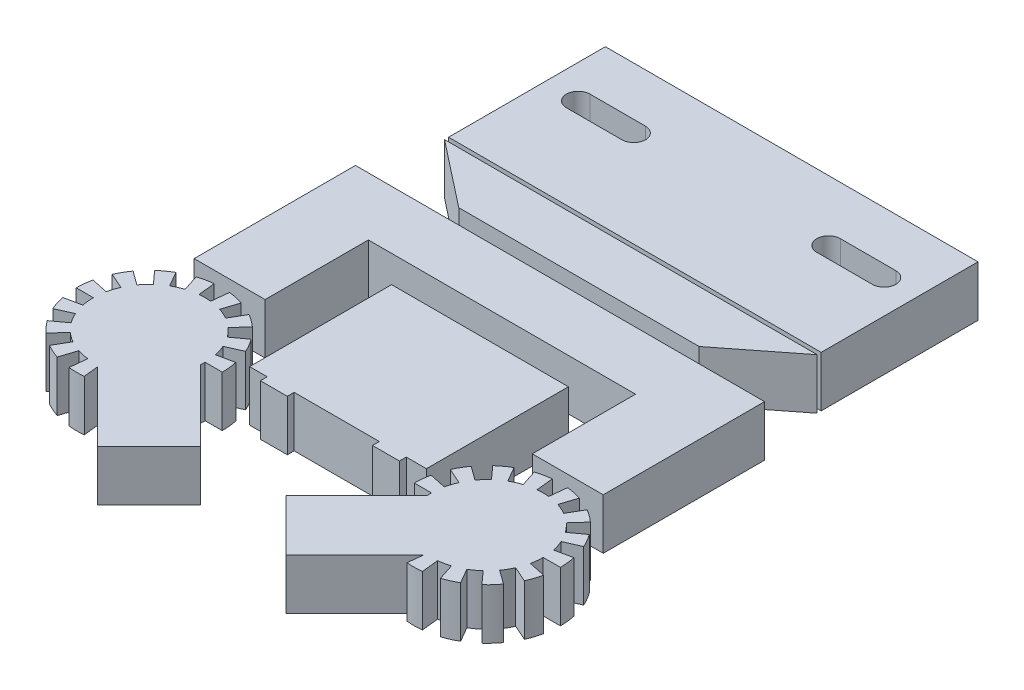
SolidWorks part; units mm, degrees
ref_plane "Front Plane" through (0, 0, 0) normal (0, 0, 1) x (1, 0, 0)
ref_plane "Top Plane" through (0, 0, 0) normal (0, 1, 0) x (1, 0, 0)
ref_plane "Right Plane" through (0, 0, 0) normal (1, 0, 0) x (0, 0, -1)
sketch "Sketch1" plane through (0, 0, 0) normal (0, 1, 0) x (1, 0, 0)
  line L0 (-41.1091, 4.4545) -> (-41.1091, 36.2727)
  line L1 (-41.1091, 36.2727) -> (39.5818, 36.2727)
  line L2 (39.5818, 36.2727) -> (39.5818, 4.4545)
  line L3 (39.5818, 4.4545) -> (25.5818, 4.4545)
  line L4 (25.5818, 4.4545) -> (25.5818, 24.8182)
  line L5 (25.5818, 24.8182) -> (-27.1091, 24.8182)
  line L6 (-27.1091, 24.8182) -> (-27.1091, 4.4545)
  line L7 (-27.1091, 4.4545) -> (-41.1091, 4.4545)
  line L8 (-32.1391, -23.6063) -> (-18.5818, -37.1636)
  line L9 (-17.1818, 19.4727) -> (17.6909, 19.4727)
  line L10 (-17.1818, 19.4727) -> (-17.1818, -8.5273)
  line L11 (-17.1818, -8.5273) -> (17.6909, -8.5273)
  line L12 (17.6909, 19.4727) -> (17.6909, -8.5273)
  line L13 (-18.5818, -37.1636) -> (-8.4, -26.9818)
  line L14 (-8.4, -26.9818) -> (-22.3545, -13.0274)
  line L15 (0, 0) -> (0, 56.6534) construction
  line L16 (23.2736, -7.685) -> (20.1863, -6.3104)
  line L17 (24.4256, -5.6897) -> (21.6916, -3.7033)
  line L18 (25.9672, -3.9776) -> (23.7059, -1.4662)
  line L55 (27.8311, -2.6234) -> (26.1414, 0.3033)
  line L56 (29.9359, -1.6863) -> (28.8916, 1.5278)
  line L57 (-22.3209, -12.1674) -> (-18.9414, -12.1674) construction
  line L58 (-22.5617, -9.8761) -> (-19.2561, -9.1735) construction
  line L60 (-22.5617, -9.8761) -> (-19.2561, -9.1735)
  line L61 (-22.3209, -12.1674) -> (-18.9414, -12.1674)
  line L67 (-32.1391, -23.6063) -> (-31.8362, -26.4886)
  line L68 (-34.4934, -23.1276) -> (-34.8466, -26.4886)
  line L69 (-36.7469, -22.6486) -> (-37.7912, -25.8627)
  line L70 (-38.8517, -21.7115) -> (-40.5414, -24.6382)
  line L71 (-40.7156, -20.3573) -> (-42.9769, -22.8687)
  line L72 (-42.2572, -18.6452) -> (-44.9912, -20.6315)
  line L73 (-43.4092, -16.6499) -> (-46.4965, -18.0244)
  line L74 (-44.1211, -14.4587) -> (-47.4267, -15.1614)
  line L75 (-44.3619, -12.1674) -> (-47.7414, -12.1674)
  line L76 (-44.1211, -9.8761) -> (-47.4267, -9.1735)
  line L77 (-43.4092, -7.685) -> (-46.4965, -6.3104)
  line L78 (-42.2572, -5.6897) -> (-44.9912, -3.7033)
  line L79 (-40.7156, -3.9776) -> (-42.9769, -1.4662)
  line L80 (-38.8517, -2.6234) -> (-40.5414, 0.3033)
  line L81 (-36.7469, -1.6863) -> (-37.7912, 1.5278)
  line L82 (-34.4934, -1.2073) -> (-34.8466, 2.1537)
  line L83 (-32.1894, -1.2073) -> (-31.8362, 2.1537)
  line L84 (-29.9359, -1.6863) -> (-28.8916, 1.5278)
  line L85 (-27.8311, -2.6234) -> (-26.1414, 0.3033)
  line L86 (-25.9672, -3.9776) -> (-23.7059, -1.4662)
  line L87 (-24.4256, -5.6897) -> (-21.6916, -3.7033)
  line L88 (-23.2736, -7.685) -> (-20.1863, -6.3104)
  line L89 (32.1894, -1.2073) -> (31.8362, 2.1537)
  line L90 (34.4934, -1.2073) -> (34.8466, 2.1537)
  line L91 (36.7469, -1.6863) -> (37.7912, 1.5278)
  line L92 (38.8517, -2.6234) -> (40.5414, 0.3033)
  line L93 (40.7156, -3.9776) -> (42.9769, -1.4662)
  line L94 (42.2572, -5.6897) -> (44.9912, -3.7033)
  line L95 (43.4092, -7.685) -> (46.4965, -6.3104)
  line L96 (22.5617, -9.8761) -> (19.2561, -9.1735) construction
  line L97 (22.3209, -12.1674) -> (18.9414, -12.1674) construction
  line L98 (44.1211, -9.8761) -> (47.4267, -9.1735)
  line L99 (44.3619, -12.1674) -> (47.7414, -12.1674)
  line L100 (44.1211, -14.4587) -> (47.4267, -15.1614)
  line L101 (43.4092, -16.6499) -> (46.4965, -18.0244)
  line L102 (42.2572, -18.6452) -> (44.9912, -20.6315)
  line L103 (40.7156, -20.3573) -> (42.9769, -22.8687)
  line L104 (38.8517, -21.7115) -> (40.5414, -24.6382)
  line L105 (36.7469, -22.6486) -> (37.7912, -25.8627)
  line L106 (34.4934, -23.1276) -> (34.8466, -26.4886)
  line L107 (32.1391, -23.6063) -> (31.8362, -26.4886)
  line L108 (22.3209, -12.1674) -> (18.9414, -12.1674)
  line L109 (22.5617, -9.8761) -> (19.2561, -9.1735)
  line L110 (8.4, -26.9818) -> (22.3545, -13.0274)
  line L111 (18.5818, -37.1636) -> (8.4, -26.9818)
  line L112 (32.1391, -23.6063) -> (18.5818, -37.1636)
  line L113 (23.7059, 39.2427) -> (-23.7059, 39.2427)
  line L114 (-23.7059, 39.2427) -> (-36.7469, 49.4769)
  line L115 (-36.7469, 49.4769) -> (36.7469, 49.4769)
  line L116 (36.7469, 50.2767) -> (-36.7469, 50.2767)
  line L117 (-36.7469, 50.2767) -> (-36.7469, 81.202)
  line L118 (-36.7469, 81.202) -> (36.7469, 81.202)
  line L119 (-30.1628, 69.2589) -> (-19.2166, 69.2589) construction
  line L122 (-30.1628, 71.5881) -> (-19.2166, 71.5881)
  line L123 (-30.1628, 66.9297) -> (-19.2166, 66.9297)
  line L124 (36.7469, 50.2767) -> (36.7469, 81.202)
  line L125 (23.7059, 39.2427) -> (36.7469, 49.4769)
  line L126 (30.1628, 69.2589) -> (19.2166, 69.2589) construction
  line L127 (30.1628, 71.5881) -> (19.2166, 71.5881)
  line L128 (30.1628, 66.9297) -> (19.2166, 66.9297)
  line L129 (13.7109, -9.8761) -> (8.4, -9.8761)
  line L130 (-13.7109, -8.5273) -> (-8.4, -8.5273)
  line L131 (-13.7109, -8.5273) -> (-13.7109, -9.8761)
  line L132 (-13.7109, -9.8761) -> (-8.4, -9.8761)
  line L133 (-8.4, -8.5273) -> (-8.4, -9.8761)
  line L134 (8.4, -8.5273) -> (8.4, -9.8761)
  line L135 (13.7109, -8.5273) -> (8.4, -8.5273)
  line L136 (13.7109, -8.5273) -> (13.7109, -9.8761)
  arc A32 (-18.9414, -12.1674) -> (-19.2561, -9.1735) centre (-33.3414, -12.1674) ccw
  arc A33 (-22.5617, -9.8761) -> (-23.2736, -7.685) centre (-33.3414, -12.1674) ccw
  arc A34 (-22.3545, -13.0274) -> (-22.3209, -12.1674) centre (-33.3414, -12.1674) ccw
  arc A41 (-34.8466, -26.4886) -> (-31.8362, -26.4886) centre (-33.3414, -12.1674) ccw
  arc A42 (-36.7469, -22.6486) -> (-34.4934, -23.1276) centre (-33.3414, -12.1674) ccw
  arc A43 (-40.5414, -24.6382) -> (-37.7912, -25.8627) centre (-33.3414, -12.1674) ccw
  arc A44 (-40.7156, -20.3573) -> (-38.8517, -21.7115) centre (-33.3414, -12.1674) ccw
  arc A45 (-44.9912, -20.6315) -> (-42.9769, -22.8687) centre (-33.3414, -12.1674) ccw
  arc A46 (-43.4092, -16.6499) -> (-42.2572, -18.6452) centre (-33.3414, -12.1674) ccw
  arc A47 (-47.4267, -15.1614) -> (-46.4965, -18.0244) centre (-33.3414, -12.1674) ccw
  arc A48 (-44.3619, -12.1674) -> (-44.1211, -14.4587) centre (-33.3414, -12.1674) ccw
  arc A49 (-47.4267, -9.1735) -> (-47.7414, -12.1674) centre (-33.3414, -12.1674) ccw
  arc A50 (-43.4092, -7.685) -> (-44.1211, -9.8761) centre (-33.3414, -12.1674) ccw
  arc A51 (-44.9912, -3.7033) -> (-46.4965, -6.3104) centre (-33.3414, -12.1674) ccw
  arc A52 (-40.7156, -3.9776) -> (-42.2572, -5.6897) centre (-33.3414, -12.1674) ccw
  arc A53 (-40.5414, 0.3033) -> (-42.9769, -1.4662) centre (-33.3414, -12.1674) ccw
  arc A54 (-36.7469, -1.6863) -> (-38.8517, -2.6234) centre (-33.3414, -12.1674) ccw
  arc A55 (-34.8466, 2.1537) -> (-37.7912, 1.5278) centre (-33.3414, -12.1674) ccw
  arc A56 (-32.1894, -1.2073) -> (-34.4934, -1.2073) centre (-33.3414, -12.1674) ccw
  arc A57 (-28.8916, 1.5278) -> (-31.8362, 2.1537) centre (-33.3414, -12.1674) ccw
  arc A58 (-27.8311, -2.6234) -> (-29.9359, -1.6863) centre (-33.3414, -12.1674) ccw
  arc A59 (-23.7059, -1.4662) -> (-26.1414, 0.3033) centre (-33.3414, -12.1674) ccw
  arc A60 (-24.4256, -5.6897) -> (-25.9672, -3.9776) centre (-33.3414, -12.1674) ccw
  arc A61 (-20.1863, -6.3104) -> (-21.6916, -3.7033) centre (-33.3414, -12.1674) ccw
  arc A62 (20.1863, -6.3104) -> (21.6916, -3.7033) centre (33.3414, -12.1674) cw
  arc A63 (24.4256, -5.6897) -> (25.9672, -3.9776) centre (33.3414, -12.1674) cw
  arc A64 (23.7059, -1.4662) -> (26.1414, 0.3033) centre (33.3414, -12.1674) cw
  arc A65 (27.8311, -2.6234) -> (29.9359, -1.6863) centre (33.3414, -12.1674) cw
  arc A66 (28.8916, 1.5278) -> (31.8362, 2.1537) centre (33.3414, -12.1674) cw
  arc A67 (32.1894, -1.2073) -> (34.4934, -1.2073) centre (33.3414, -12.1674) cw
  arc A68 (34.8466, 2.1537) -> (37.7912, 1.5278) centre (33.3414, -12.1674) cw
  arc A69 (36.7469, -1.6863) -> (38.8517, -2.6234) centre (33.3414, -12.1674) cw
  arc A70 (40.5414, 0.3033) -> (42.9769, -1.4662) centre (33.3414, -12.1674) cw
  arc A71 (40.7156, -3.9776) -> (42.2572, -5.6897) centre (33.3414, -12.1674) cw
  arc A72 (44.9912, -3.7033) -> (46.4965, -6.3104) centre (33.3414, -12.1674) cw
  arc A73 (47.4267, -9.1735) -> (47.7414, -12.1674) centre (33.3414, -12.1674) cw
  arc A74 (47.4267, -15.1614) -> (46.4965, -18.0244) centre (33.3414, -12.1674) cw
  arc A75 (43.4092, -7.685) -> (44.1211, -9.8761) centre (33.3414, -12.1674) cw
  arc A76 (44.3619, -12.1674) -> (44.1211, -14.4587) centre (33.3414, -12.1674) cw
  arc A77 (43.4092, -16.6499) -> (42.2572, -18.6452) centre (33.3414, -12.1674) cw
  arc A78 (44.9912, -20.6315) -> (42.9769, -22.8687) centre (33.3414, -12.1674) cw
  arc A79 (40.7156, -20.3573) -> (38.8517, -21.7115) centre (33.3414, -12.1674) cw
  arc A80 (40.5414, -24.6382) -> (37.7912, -25.8627) centre (33.3414, -12.1674) cw
  arc A81 (36.7469, -22.6486) -> (34.4934, -23.1276) centre (33.3414, -12.1674) cw
  arc A82 (34.8466, -26.4886) -> (31.8362, -26.4886) centre (33.3414, -12.1674) cw
  arc A83 (22.3545, -13.0274) -> (22.3209, -12.1674) centre (33.3414, -12.1674) cw
  arc A84 (22.5617, -9.8761) -> (23.2736, -7.685) centre (33.3414, -12.1674) cw
  arc A85 (18.9414, -12.1674) -> (19.2561, -9.1735) centre (33.3414, -12.1674) cw
  arc A88 (-30.1628, 71.5881) -> (-30.1628, 66.9297) centre (-30.1628, 69.2589) ccw
  arc A89 (-19.2166, 66.9297) -> (-19.2166, 71.5881) centre (-19.2166, 69.2589) ccw
  arc A90 (30.1628, 71.5881) -> (30.1628, 66.9297) centre (30.1628, 69.2589) cw
  arc A91 (19.2166, 66.9297) -> (19.2166, 71.5881) centre (19.2166, 69.2589) cw
  point P38 (-33.2182, -12.3455)
  point P152 (-33.3414, -12.1674)
  point P186 (33.3414, -12.1674)
  point P187 (33.2182, -12.3455)
  point P197 (-24.6897, 69.2589)
  point P203 (0, 50.2767)
  point P204 (0, 81.202)
  point P205 (0, 49.4769)
  point P206 (0, 39.2427)
  point P208 (24.6897, 69.2589)
extrude "Boss-Extrude1" add sketch "Sketch1" along normal blind 10 contours L88 A61 L87 A60 L86 A59 L85 A58 L84 A57 L83 A56 L82 A55 L81 A54 L80 A53 L79 A52 L78 A51 L77 A50 L76 A49 L75 A48 L74 A47 L73 A46 L72 A45 L71 A44 L70 A43 L69 A42 L68 A41 L67 L8 L13 L14 A34 L61 A32 L60 A33 | A85 L108 A83 L110 L111 L112 L107 A82 L106 A81 L105 A80 L104 A79 L103 A78 L102 A77 L101 A74 L100 A76 L99 A73 L98 A75 L95 A72 L94 A71 L93 A70 L92 A69 L91 A68 L90 A67 L89 A66 L56 A65 L55 A64 L18 A63 L17 A62 L16 A84 L109 | L12 L9 L10 L11 | L7 L6 L5 L4 L3 L2 L1 L0 | L113 L125 L115 L114 | L116 L124 L118 L117 A89 L123 A88 L122 L128 A91 L127 A90 | L133 L11 L131 L132 | L136 L11 L134 L129
